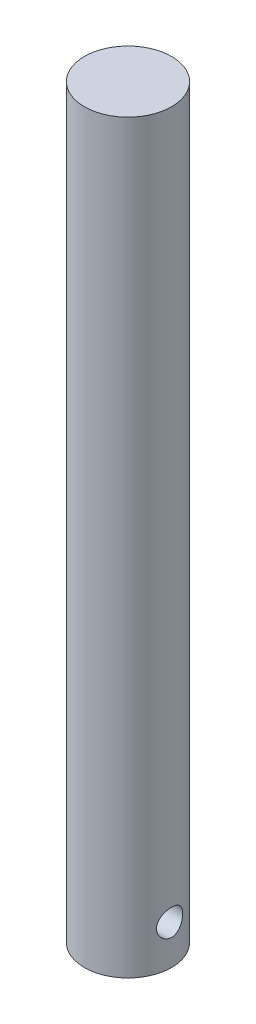
SolidWorks part; units mm, degrees
ref_plane "Alzado" through (0, 0, 0) normal (0, 0, 1) x (1, 0, 0)
ref_plane "Planta" through (0, 0, 0) normal (0, 1, 0) x (1, 0, 0)
ref_plane "Vista lateral" through (0, 0, 0) normal (1, 0, 0) x (0, 0, -1)
sketch "Croquis1" plane through (0, 0, 0) normal (0, 1, 0) x (1, 0, 0)
  circle A0 centre (0, 0) radius 10
  dimension "D1" = 20
extrude "Saliente-Extruir1" add sketch "Croquis1" along normal blind 150 and the other way blind 21
sketch "Croquis2" plane through (0, 0, 0) normal (1, 0, 0) x (0, 0, -1)
  line L0 (-10, -21) -> (10, -21) construction
  circle A0 centre (0, -12) radius 3
  dimension "D1" = 6
  dimension "D2" = 9
extrude "Cortar-Extruir1" cut sketch "Croquis2" against normal mid plane 25
